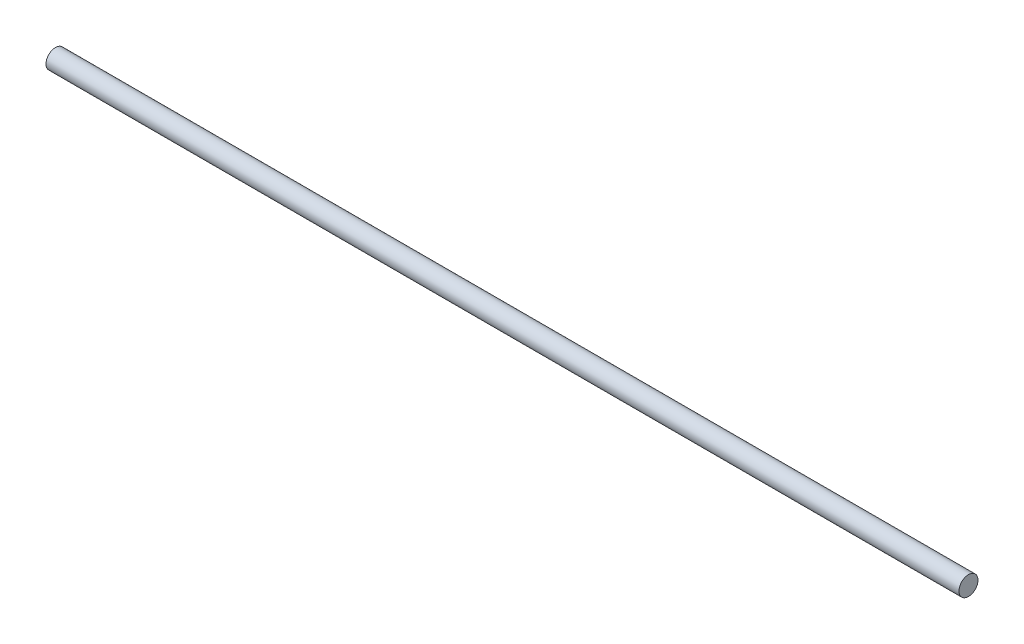
SolidWorks part; units mm, degrees
ref_plane "Front Plane" through (0, 0, 0) normal (0, 0, 1) x (1, 0, 0)
ref_plane "Top Plane" through (0, 0, 0) normal (0, 1, 0) x (1, 0, 0)
ref_plane "Right Plane" through (0, 0, 0) normal (1, 0, 0) x (0, 0, -1)
sketch "Sketch1" plane through (0, 0, 0) normal (1, 0, 0) x (0, 0, -1)
  circle A0 centre (0, 0) radius 5
  dimension "D1" = 10
extrude "Boss-Extrude1" add sketch "Sketch1" along normal mid plane 480
